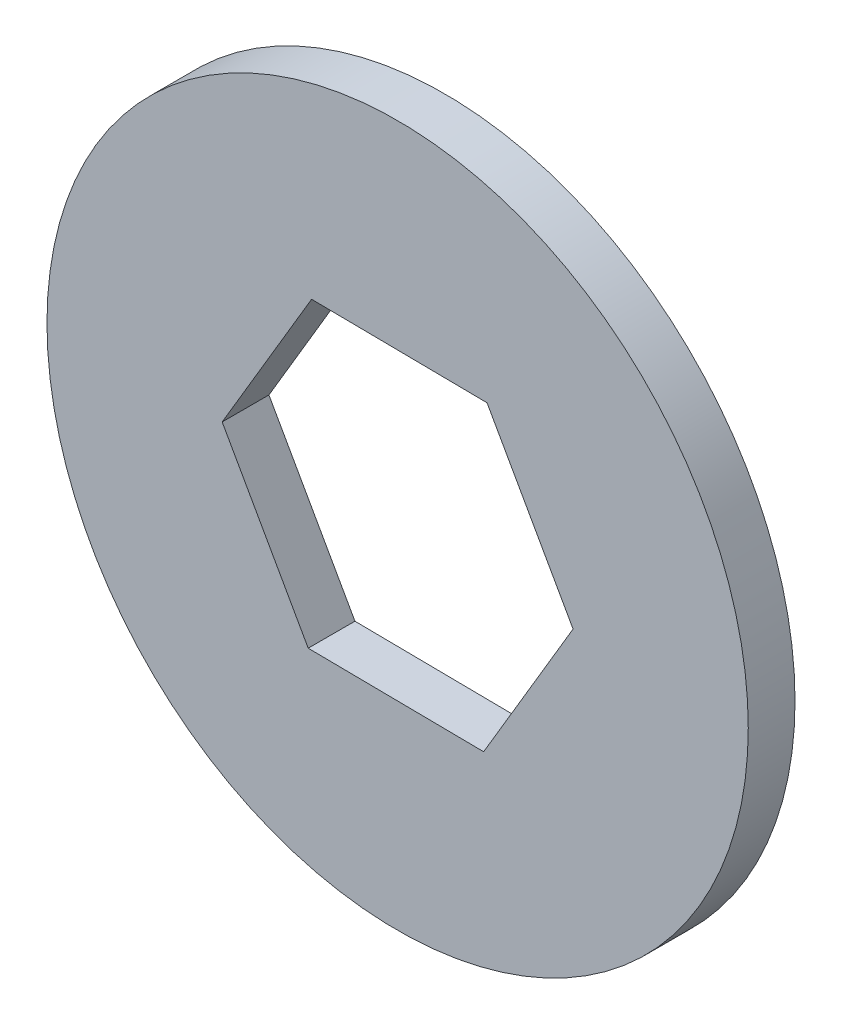
SolidWorks part; units mm, degrees
ref_plane "Alzado" through (0, 0, 0) normal (0, 0, 1) x (1, 0, 0)
ref_plane "Planta" through (0, 0, 0) normal (0, 1, 0) x (1, 0, 0)
ref_plane "Vista lateral" through (0, 0, 0) normal (1, 0, 0) x (0, 0, -1)
sketch "Croquis1" plane through (0, 0, 0) normal (0, 0, 1) x (1, 0, 0)
  line L1 (3.68, -6.5415) -> (7.5051, -0.0838)
  line L2 (7.5051, -0.0838) -> (3.8251, 6.4577)
  line L3 (3.8251, 6.4577) -> (-3.68, 6.5415)
  line L4 (-3.68, 6.5415) -> (-7.5051, 0.0838)
  line L5 (-7.5051, 0.0838) -> (-3.8251, -6.4577)
  line L6 (-3.8251, -6.4577) -> (3.68, -6.5415)
  circle A0 centre (0, 0) radius 6.5 construction
  circle A1 centre (0, 0) radius 15
  dimension "D2" = 30
  dimension "D1" = 13
extrude "Saliente-Extruir1" add sketch "Croquis1" along normal blind 2
